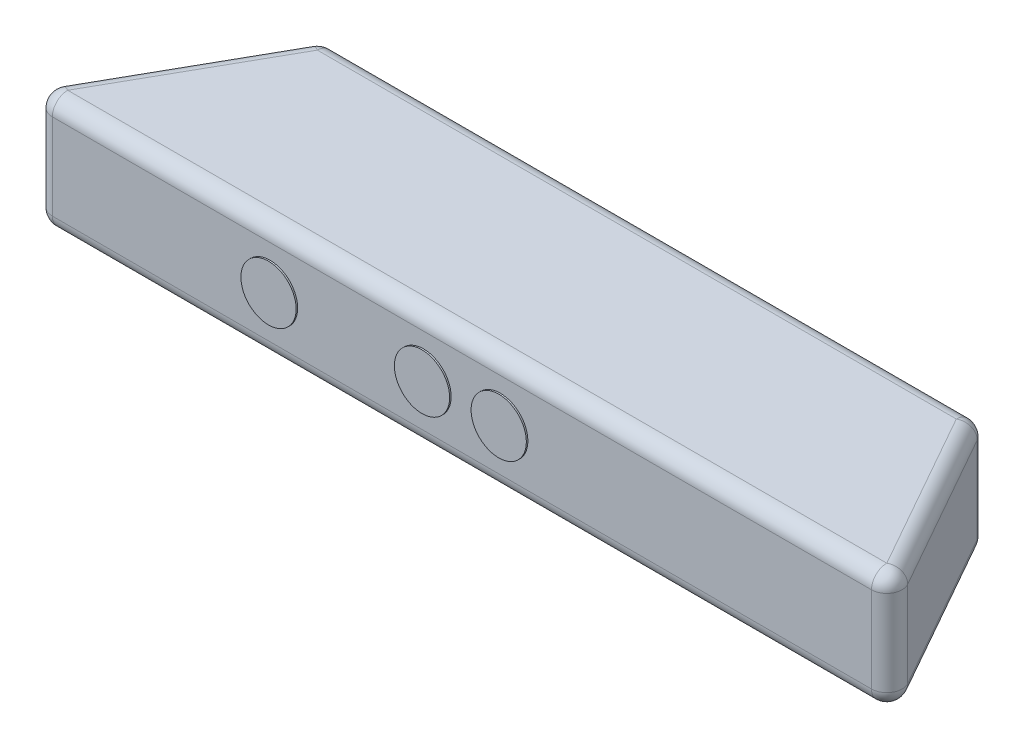
SolidWorks part; units mm, degrees
material "ABS"
ref_plane "Front Plane" through (0, 0, 0) normal (0, 0, 1) x (1, 0, 0)
ref_plane "Top Plane" through (0, 0, 0) normal (0, 1, 0) x (1, 0, 0)
ref_plane "Right Plane" through (0, 0, 0) normal (1, 0, 0) x (0, 0, -1)
sketch "Sketch1" plane through (0, 0, 0) normal (0, 1, 0) x (1, 0, 0)
  line L0 (-142, 0) -> (142, 0)
  line L1 (142, 0) -> (107, 62)
  line L2 (107, 62) -> (-107, 62)
  line L3 (-107, 62) -> (-142, 0)
  line L4 (0, 0) -> (0, 62) construction
  dimension "D1" = 62
  dimension "D2" = 284
  dimension "D3" = 214
extrude "Boss-Extrude1" add sketch "Sketch1" along normal blind 38
sketch "Sketch2" plane through (0, 0, 0) normal (0, -1, 0) x (1, 0, 0)
  line L0 (0, 0) -> (0, -62) construction
  line L1 (107, -62) -> (-107, -62) construction
  line L2 (8.5, -31) -> (-8.5, -31) construction
  line L3 (0, -35.75) -> (0, -31) construction
  arc A0 (8.5, -31) -> (-8.5, -31) centre (0, -25.7697) cw
  arc A1 (8.5, -31) -> (-8.5, -31) centre (0, -36.2303) ccw
  dimension "D1" = 4.75
  dimension "D2" = 17
extrude "Boss-Extrude2" add sketch "Sketch2" along normal blind 10
fillet "Fillet1" radius 5 12 edges at (-142, 19, 0) (-124.5, 38, -31) (-107, 19, -62) (-124.5, 0, -31) (0, 0, -62) (0, 38, -62) (0, 38, 0) (124.5, 38, -31) (107, 19, -62) (142, 19, 0) (124.5, 0, -31) (0, 0, 0)
sketch "Sketch3" plane through (0, 0, 0) normal (0, 0, 1) x (1, 0, 0)
  line L0 (0, 5) -> (0, 33) construction
  line L1 (-133.4357, 5) -> (133.4357, 5) construction
  line L2 (133.4357, 33) -> (-133.4357, 33) construction
  line L3 (-133.4357, 19) -> (133.4357, 19) construction
  line L4 (-133.4357, 33) -> (-133.4357, 5) construction
  line L5 (133.4357, 5) -> (133.4357, 33) construction
  circle A0 centre (12.5, 19) radius 9
  circle A1 centre (-12.5, 19) radius 9
  circle A2 centre (-62.5, 19) radius 9
  dimension "D1" = 18
  dimension "D2" = 25
  dimension "D3" = 50
extrude "Cut-Extrude1" cut sketch "Sketch3" against normal blind 5
sketch "Sketch5" plane through (0, 0, 0) normal (0, 0, 1) x (1, 0, 0)
  circle A0 centre (-12.5, 19) radius 9 construction
  circle A1 centre (12.5, 19) radius 9 construction
  circle A2 centre (-62.5, 19) radius 9 construction
  circle A3 centre (-12.5, 19) radius 9
  circle A4 centre (12.5, 19) radius 9
  circle A5 centre (-62.5, 19) radius 9
  circle A6 centre (-12.5, 19) radius 9
  circle A7 centre (12.5, 19) radius 9
  circle A8 centre (-62.5, 19) radius 9
extrude "Boss-Extrude3" add sketch "Sketch5" against normal mid plane 1 contours A5 | A3
sketch "Sketch6" plane through (0, 0, 0) normal (0, -1, 0) x (1, 0, 0)
  line L0 (0, -5) -> (0, -57) construction
  line L1 (133.4357, -5) -> (-133.4357, -5) construction
  line L2 (-104.0809, -57) -> (104.0809, -57) construction
  line L3 (-133.4357, 0) -> (133.4357, 0) construction
  circle A0 centre (-97, -17.5) radius 3
  circle A1 centre (97, -17.5) radius 3
  dimension "D3" = 6
  dimension "D1" = 17.5
  dimension "D2" = 97
extrude "Cut-Extrude2" cut sketch "Sketch6" against normal blind 2.5
sketch "Sketch7" plane through (0, 0, 0) normal (0, 0, 1) x (1, 0, 0)
  line L0 (133.4357, 19) -> (0, 19) construction
  line L1 (133.4357, 5) -> (133.4357, 33) construction
  line L2 (0, 19) -> (0, 5) construction
  line L3 (-133.4357, 5) -> (133.4357, 5) construction
